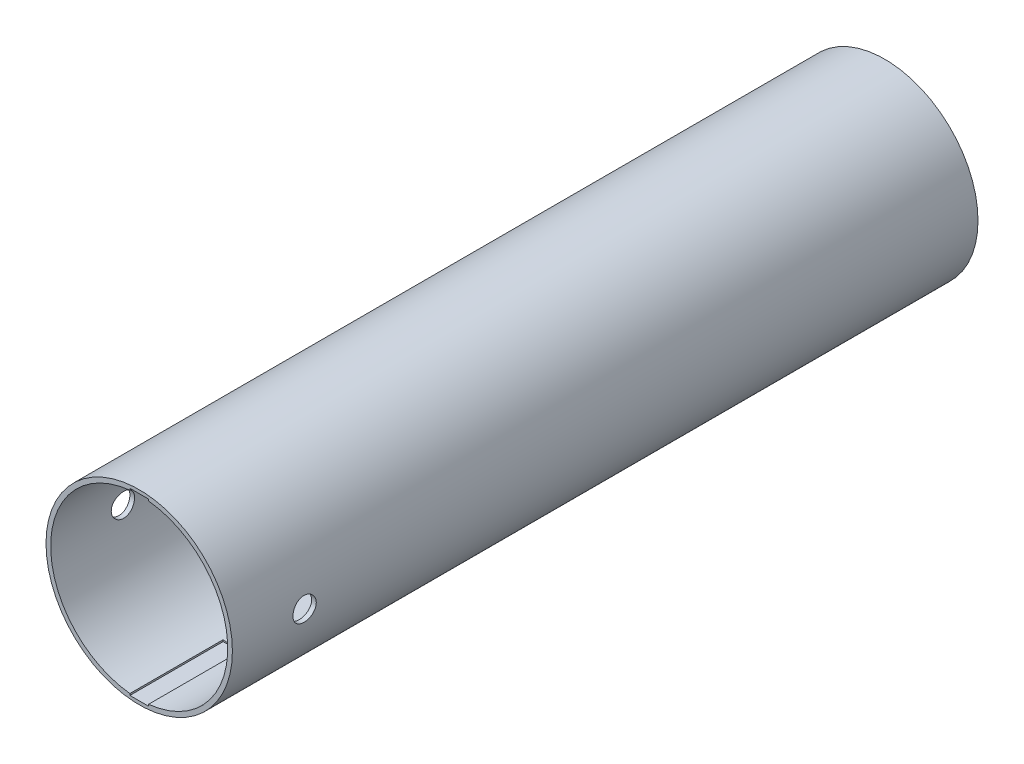
SolidWorks part; units mm, degrees
material "Ti-6Al-4VSolution treated and aged (SS)"
ref_plane "Front Plane" through (0, 0, 0) normal (0, 0, 1) x (1, 0, 0)
ref_plane "Top Plane" through (0, 0, 0) normal (0, 1, 0) x (1, 0, 0)
ref_plane "Right Plane" through (0, 0, 0) normal (1, 0, 0) x (0, 0, -1)
sketch "Sketch1" plane through (0, 0, 0) normal (0, 0, 1) x (1, 0, 0)
  circle A0 centre (0, 0) radius 10
  dimension "D1" = 20
extrude "Boss-Extrude1" add sketch "Sketch1" along normal blind 80
shell "Shell1" thickness 0.5
ref_plane "Plane1" through (10, 0, 0) normal (1, 0, 0) x (0, 0, -1)
ref_plane "Plane3" through (-10, 0, 0) normal (1, 0, 0) x (0, 0, -1)
sketch "Sketch4" plane through (10, 0, 0) normal (1, 0, 0) x (0, 0, -1)
  line L0 (-80, 10) -> (-80, -10) construction
  circle A0 centre (-72.25, 0) radius 1.25
  dimension "D1" = 2.5
  dimension "D2" = 7.75
extrude "Cut-Extrude3" cut sketch "Sketch4" against normal through all
ref_plane "Plane5" through (0, 0, 80) normal (0, 0, 1) x (1, 0, 0)
sketch "Sketch8" plane through (0, 0, 80) normal (0, 0, 1) x (1, 0, 0)
  line L0 (0, 12.6823) -> (0, -11.6755) construction
  line L1 (-12.0889, 0) -> (17.2868, 0) construction
  line L2 (-1, -9.375) -> (1, -9.375)
  line L3 (-1, 9.625) -> (1, 9.625)
  line L4 (-1, 9.625) -> (-1, 9.375)
  line L5 (-1, 9.375) -> (1, 9.375)
  line L6 (1, 9.625) -> (1, 9.375)
  line L7 (-1, 9.625) -> (1, 9.375) construction
  line L8 (-1, 9.375) -> (1, 9.625) construction
  line L9 (1, -9.625) -> (1, -9.375)
  line L10 (-1, -9.625) -> (1, -9.625)
  line L11 (-1, -9.625) -> (-1, -9.375)
  circle A0 centre (0, 0) radius 9.5 construction
  point P5 (0, 9.5)
  dimension "D1" = 0.25
  dimension "D2" = 2
extrude "Cut-Extrude5" cut sketch "Sketch8" against normal blind 10
